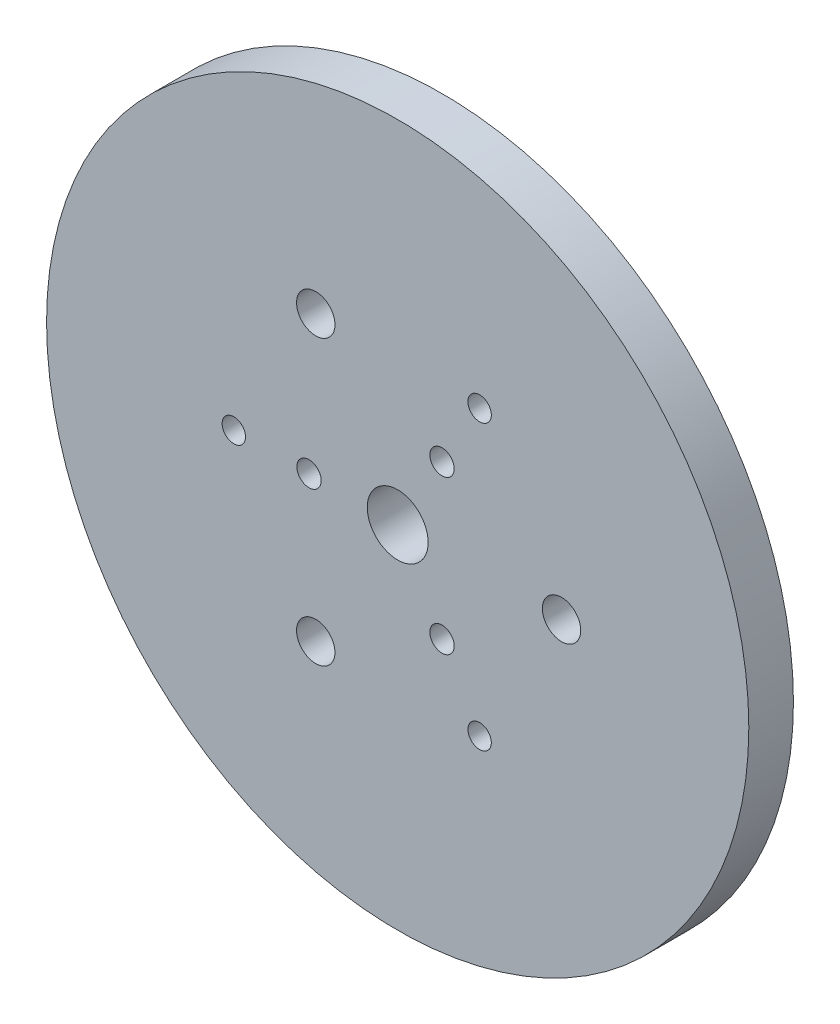
SolidWorks part; units mm, degrees
ref_plane "Alzado" through (0, 0, 0) normal (0, 0, 1) x (1, 0, 0)
ref_plane "Planta" through (0, 0, 0) normal (0, 1, 0) x (1, 0, 0)
ref_plane "Vista lateral" through (0, 0, 0) normal (1, 0, 0) x (0, 0, -1)
sketch "Croquis1" plane through (0, 0, 0) normal (0, 0, 1) x (1, 0, 0)
  circle A0 centre (0, 0) radius 75
  dimension "D1" = 150
extrude "Saliente-Extruir1" add sketch "Croquis1" along normal blind 9.53
sketch "Croquis2" plane through (0, 0, 0) normal (0, 0, -1) x (-1, 0, 0)
  circle A1 centre (-35, 0) radius 4.1
  circle A2 centre (17.5, 30.3109) radius 4.1
  circle A3 centre (17.5, -30.3109) radius 4.1
  point P12 (0, 0)
  dimension "D2" = 8.2
  dimension "D3" = 3
extrude "Cortar-Extruir1" cut sketch "Croquis2" against normal up to next
sketch "Croquis3" plane through (0, 0, 0) normal (0, 0, -1) x (-1, 0, 0)
  circle A0 centre (0, 0) radius 6.5
  dimension "D1" = 13
extrude "Cortar-Extruir2" cut sketch "Croquis3" against normal up to next
sketch "Croquis4" plane through (0, 0, 9.53) normal (0, 0, 1) x (1, 0, 0)
  line L0 (-18.9371, 0) -> (0, 0) construction
  circle A1 centre (-18.9371, 0) radius 2.6
  circle A2 centre (9.4685, 16.4) radius 2.6
  circle A3 centre (9.4685, -16.4) radius 2.6
  point P12 (0, 0)
  dimension "D3" = 5.2
  dimension "D2" = 32.8
  dimension "D1" = 3
extrude "Cortar-Extruir3" cut sketch "Croquis4" against normal up to next
sketch "Croquis5" plane through (0, 0, 9.53) normal (0, 0, 1) x (1, 0, 0)
  line L0 (-35, 0) -> (0, 0) construction
  line L1 (17.5, 30.3109) -> (-35, 0) construction
  line L2 (17.5, 30.3109) -> (17.5, -30.3109) construction
  line L3 (17.5, -30.3109) -> (-35, 0) construction
  circle A1 centre (-35, 0) radius 2.5
  circle A2 centre (17.5, 30.3109) radius 2.5
  circle A3 centre (17.5, -30.3109) radius 2.5
  point P12 (0, 0)
  dimension "D1" = 5
  dimension "D3" = 60.6218
  dimension "D4" = 35
  dimension "D2" = 3
extrude "Cortar-Extruir4" cut sketch "Croquis5" against normal up to next
